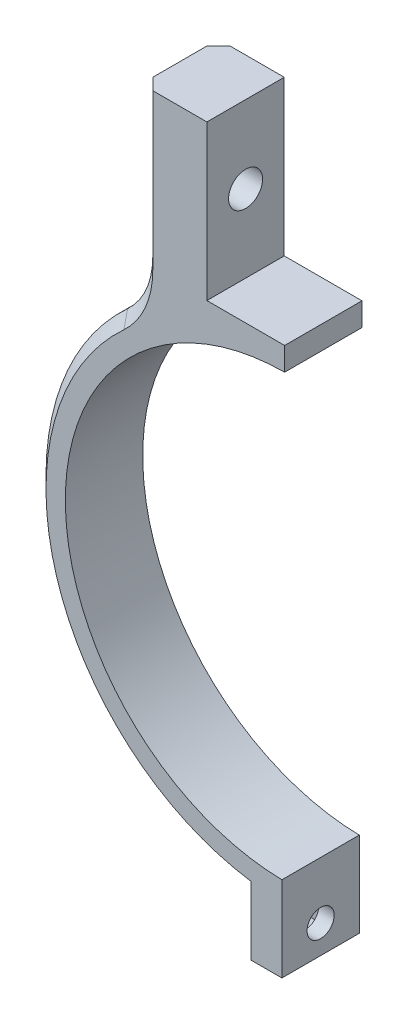
SolidWorks part; units mm, degrees
ref_plane "Ebene vorne" through (0, 0, 0) normal (0, 0, 1) x (1, 0, 0)
ref_plane "Ebene oben" through (0, 0, 0) normal (0, 1, 0) x (1, 0, 0)
ref_plane "Ebene rechts" through (0, 0, 0) normal (1, 0, 0) x (0, 0, -1)
sketch "Skizze1" plane through (0, 0, 0) normal (0, 0, 1) x (1, 0, 0)
  line L0 (0, 0) -> (0, 53.7291) construction
  line L14 (0, 0) -> (0, -44.1347) construction
  line L15 (0.5, -28.4956) -> (0.5, -32.4962)
  line L16 (-0.5, -28.4956) -> (-0.5, -32.4962)
  line L17 (0.5, -32.4962) -> (0.5, -39.4962)
  line L18 (0.5, -39.4962) -> (4.5, -39.4962)
  line L19 (4.5, -39.4962) -> (4.5, -32.187)
  line L20 (-4.5, -39.4962) -> (-4.5, -32.187)
  line L21 (-0.5, -39.4962) -> (-4.5, -39.4962)
  line L22 (-0.5, -32.4962) -> (-0.5, -39.4962)
  line L23 (-10.2, 31.5) -> (-10.2, 51.5)
  line L24 (-10.2, 51.5) -> (-18.7, 51.5)
  line L25 (-18.7, 51.5) -> (-18.7, 26.5812)
  line L26 (-10.2, 31.5) -> (10.2, 31.5)
  line L27 (0, 28.5) -> (12.0002, 28.5) construction
  line L28 (18.7, 51.5) -> (18.7, 26.5812)
  line L29 (10.2, 51.5) -> (18.7, 51.5)
  line L30 (10.2, 31.5) -> (10.2, 51.5)
  arc A0 (0.5, -28.4956) -> (-0.5, -28.4956) centre (0, 0) ccw
  arc A1 (-18.7, 26.5812) -> (-4.5, -32.187) centre (0, 0) ccw
  arc A2 (4.5, -32.187) -> (18.7, 26.5812) centre (0, 0) ccw
  point P10 (0, 33.5025)
  point P11 (0, 31.6594)
  point P17 (0, 31.5)
  point P18 (0, 39.6025)
  dimension "D1" = 57
  dimension "D2" = 4
  dimension "D3" = 20.4
  dimension "D4" = 20
  dimension "D5" = 3
  dimension "D6" = 8.5
  dimension "D10" = 1
  dimension "D11" = 4
  dimension "D12" = 7
extrude "Aufsatz-Linear austragen1" add sketch "Skizze1" along normal blind 10
sketch "Skizze2" plane through (-4.5, 0, 0) normal (-1, 0, 0) x (0, 0, 1)
  line L0 (0, -35.8416) -> (10, -35.8416) construction
  line L1 (0, -32.187) -> (0, -39.4962) construction
  line L2 (10, -32.187) -> (10, -39.4962) construction
  circle A0 centre (5, -35.8416) radius 1.75
  dimension "D1" = 3.5
extrude "Schnitt-Linear austragen1" cut sketch "Skizze2" against normal through all
sketch "Skizze3" plane through (0, 0, 10) normal (0, 0, 1) x (1, 0, 0)
  line L0 (-10.8174, 36.4205) -> (0, 26.8755)
  line L1 (0, 26.8755) -> (11.8484, 37.1414)
  line L2 (11.8484, 37.1414) -> (47.3746, 17.8863)
  line L3 (47.3746, 17.8863) -> (51.4546, -59.0738)
  line L4 (51.4546, -59.0738) -> (-81.1349, -43.2704)
  line L5 (-81.1349, -43.2704) -> (-40.9452, 68.8874)
  line L6 (-40.9452, 68.8874) -> (-10.8174, 36.4205)
extrude "Schnitt-Linear austragen2" [suppressed] cut sketch "Skizze3" against normal through all
sketch "Skizze4" plane through (-18.7, 0, 0) normal (-1, 0, 0) x (0, 0, 1)
  line L0 (5, 51.5) -> (5, 31.5) construction
  line L1 (10, 51.5) -> (0, 51.5) construction
  line L3 (10, 31.5) -> (0, 31.5) construction
  circle A0 centre (5, 41.5) radius 2.2
  dimension "D1" = 4.4
extrude "Schnitt-Linear austragen3" cut sketch "Skizze4" against normal through all
fillet "Verrundung1" radius 10 2 edges at (18.7, 26.5812, 5) (-18.7, 26.5812, 5)
sketch "Skizze5" plane through (-4.5, 0, 0) normal (-1, 0, 0) x (0, 0, 1)
  line L1 (2.25, -38.5916) -> (7.75, -38.5916)
  line L2 (2.25, -38.5916) -> (2.25, -33.0916)
  line L3 (2.25, -33.0916) -> (7.75, -33.0916)
  line L4 (7.75, -38.5916) -> (7.75, -33.0916)
  line L5 (2.25, -38.5916) -> (7.75, -33.0916) construction
  line L6 (2.25, -33.0916) -> (7.75, -38.5916) construction
  point P0 (5, -35.8416)
  dimension "D1" = 5.5
extrude "Schnitt-Linear austragen4" cut sketch "Skizze5" against normal blind 2
chamfer "Fase1" distance 1.5 angle 45 12 edges at (-18.7, 41.4229, 0) (-18.7, 41.4229, 10) (-19.5477, 27.3165, 10) (-19.5477, 27.3165, 0) (-31.0366, -9.6425, 10) (-31.0366, -9.6425, 0) (18.7, 41.4229, 10) (18.7, 41.4229, 0) (19.5477, 27.3165, 10) (19.5477, 27.3165, 0) (31.0366, -9.6425, 0) (31.0366, -9.6425, 10)
sketch "Skizze6" plane through (0, 0, 0) normal (0, 0, 1) x (1, 0, 0)
  line L0 (0, -80.0659) -> (0, 27.4786)
  line L1 (0, 80.0659) -> (51.6949, 80.0659)
  line L2 (51.6949, 80.0659) -> (51.6949, -72.9797)
  line L3 (51.6949, -72.9797) -> (0, -80.0659)
  line L4 (0, 27.4786) -> (-0.15, 27.4786)
  line L5 (-0.15, 27.4786) -> (-0.15, 32.4289)
  line L6 (-0.15, 32.4289) -> (0, 32.4289)
  line L7 (0, 32.4289) -> (0, 80.0659)
  point P4 (0, 0)
  dimension "D1" = 0.15
extrude "Schnitt-Linear austragen5" cut sketch "Skizze6" along normal through all
